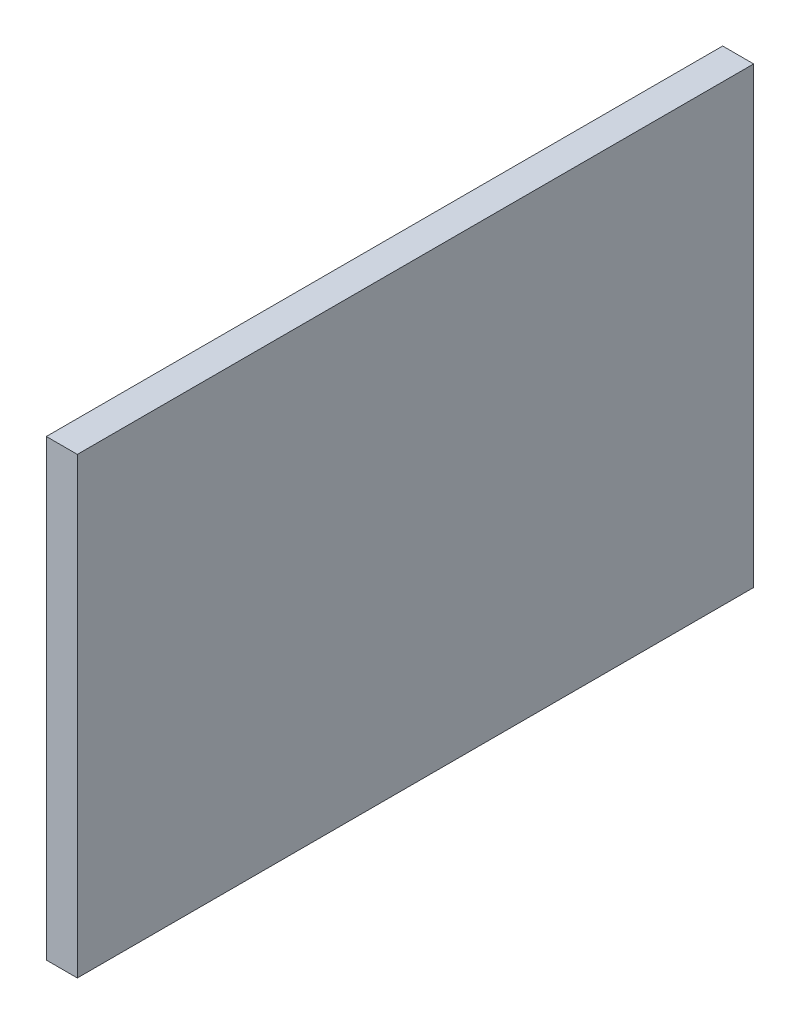
SolidWorks part; units mm, degrees
ref_plane "Front Plane" through (0, 0, 0) normal (1, 0, 0) x (0, 1, 0)
ref_plane "Top Plane" through (0, 0, 0) normal (0, 0, 1) x (0, 1, 0)
ref_plane "Right Plane" through (0, 0, 0) normal (0, 1, 0) x (-1, 0, 0)
sketch "Sketch1" plane through (0, 0, 0) normal (1, 0, 0) x (0, 1, 0)
  line L0 (69.57, 90.48) -> (69.57, 125.38) construction
  line L1 (46.17, 125.38) -> (69.57, 125.38)
  line L2 (46.17, 125.38) -> (46.17, 90.48)
  line L3 (46.17, 90.48) -> (69.57, 90.48)
  line L4 (69.57, 125.38) -> (69.57, 90.48)
  point P7 (69.57, 90.48)
extrude "Boss-Extrude1" add sketch "Sketch1" along normal up to vertex (1.6 mm away) contours L2 L1 L4 L3
